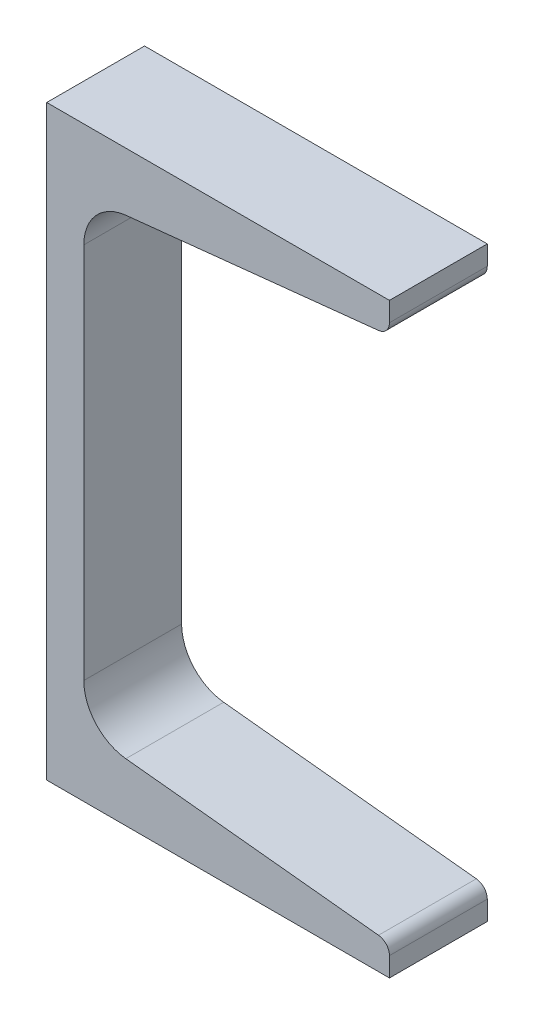
SolidWorks part; units mm, degrees
ref_plane "Plane1" through (0, 0, 0) normal (0, 0, 1) x (1, 0, 0)
ref_plane "Plane2" through (0, 0, 0) normal (0, 1, 0) x (-1, 0, 0)
ref_plane "Plane3" through (0, 0, 0) normal (1, 0, 0) x (0, 0, -1)
sketch "Sketch1" plane through (0, 0, 0) normal (0, 0, 1) x (1, 0, 0)
  line L0 (89.0016, 152.4) -> (0, 152.4)
  line L1 (89.0016, 0) -> (0, 0)
  line L2 (0, 152.4) -> (0, 0)
  line L3 (7.8492, 0) -> (-7.8492, 0) construction
  line L4 (0, -15.6984) -> (0, 15.6984) construction
  line L5 (0, 12.065) -> (89.0016, 12.065) construction
  line L6 (89.0016, 152.4) -> (89.0016, 144.5063)
  line L7 (89.0016, 0) -> (89.0016, 7.8937)
  line L12 (9.6266, 125.1859) -> (9.6266, 27.2141)
  line L17 (20.5442, 137.3112) -> (89.0016, 144.5063)
  line L18 (20.5442, 15.0888) -> (89.0016, 7.8937)
  arc A9 (9.6266, 27.2141) -> (20.5442, 15.0888) centre (21.8186, 27.2141) ccw
  arc A10 (9.6266, 125.1859) -> (20.5442, 137.3112) centre (21.8186, 125.1859) cw
  dimension "RI" = 12.192
  dimension "D2" = 6
  dimension "D3" = 27.2141
  dimension "Depth" = 152.4
  dimension "BF" = 89.0016
  dimension "TW" = 9.6266
  dimension "TF" = 12.065
  dimension "d1" = 97.9719
extrude "BaseMchannel" add sketch "Sketch1" along normal mid plane 25.4
fillet "ToeFillet" radius 3.175 2 edges at (89.0016, 7.8937, 0) (89.0016, 144.5063, 0)
equation "\"d1@Sketch1\" = \"Depth@Sketch1\" - 2*\"TF@Sketch1\" -  2*( \"RI@Sketch1\" * cos(\"D2@Sketch1\"/180*3.141592654))-2*((((\"BF@Sketch1\"-\"TW@Sketch1\")/2)-(\"RI@Sketch1\"-\"RI@Sketch1\"*sin(\"D2@Sketch1\"/180*3.141592654)))*tan(\"D2@Sketch1\"/180*3.141592654))"
equation "\"D3@Sketch1\" =  ( \"Depth@Sketch1\" - \"d1@Sketch1\" )  / 2"
